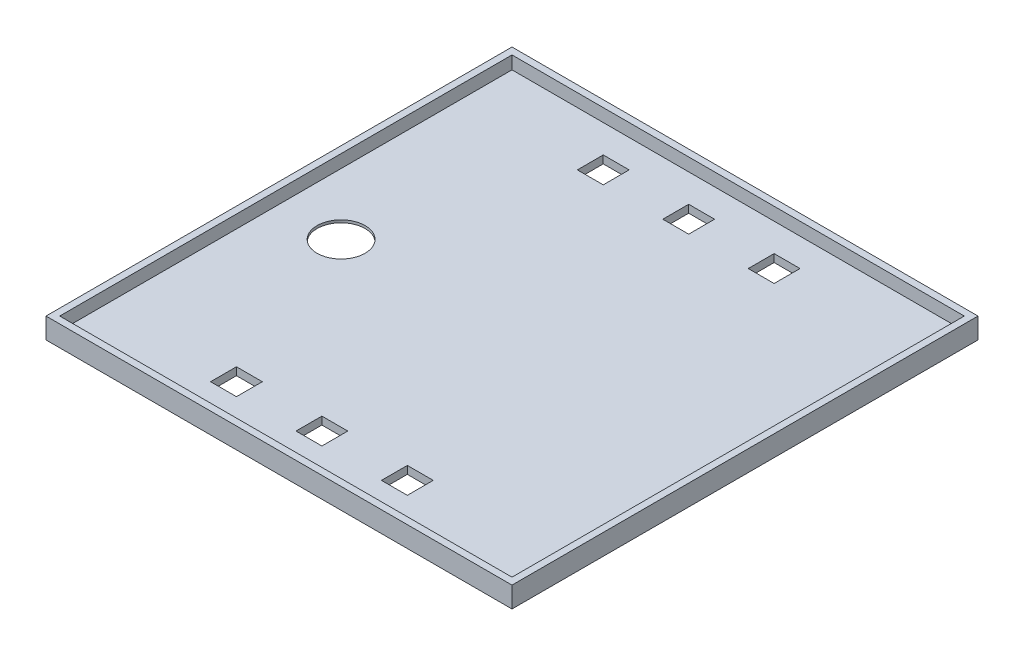
SolidWorks part; units mm, degrees
ref_plane "Front Plane" through (0, 0, 0) normal (0, 0, 1) x (1, 0, 0)
ref_plane "Top Plane" through (0, 0, 0) normal (0, 1, 0) x (1, 0, 0)
ref_plane "Right Plane" through (0, 0, 0) normal (1, 0, 0) x (0, 0, -1)
sketch "Sketch1" plane through (0, 0, 0) normal (0, 1, 0) x (1, 0, 0)
  line L1 (-45, -45) -> (45, -45)
  line L2 (-45, -45) -> (-45, 45)
  line L3 (-45, 45) -> (45, 45)
  line L4 (45, -45) -> (45, 45)
  line L5 (-45, -45) -> (45, 45) construction
  line L6 (-45, 45) -> (45, -45) construction
  point P0 (0, 0)
  dimension "D1" = 90
  dimension "D2" = 90
extrude "Boss-Extrude1" add sketch "Sketch1" along normal blind 4
sketch "Sketch2" plane through (0, 4, 0) normal (0, 1, 0) x (1, 0, 0)
  line L1 (-43.675, -43.675) -> (43.675, -43.675)
  line L2 (-43.675, -43.675) -> (-43.675, 43.675)
  line L3 (-43.675, 43.675) -> (43.675, 43.675)
  line L4 (43.675, -43.675) -> (43.675, 43.675)
  line L5 (-43.675, -43.675) -> (43.675, 43.675) construction
  line L6 (-43.675, 43.675) -> (43.675, -43.675) construction
  point P0 (0, 0)
  dimension "D1" = 87.35
  dimension "D2" = 87.35
extrude "Cut-Extrude2" cut sketch "Sketch2" against normal blind 2.5
sketch "Sketch6" plane through (0, 0, 0) normal (0, -1, 0) x (1, 0, 0)
  line L1 (17.3668, -38.2575) -> (12.3668, -38.2575)
  line L2 (17.3668, -38.2575) -> (17.3668, -33.2575)
  line L3 (17.3668, -33.2575) -> (12.3668, -33.2575)
  line L4 (12.3668, -38.2575) -> (12.3668, -33.2575)
  line L5 (0.8662, -38.2575) -> (-4.1338, -38.2575)
  line L6 (0.8662, -38.2575) -> (0.8662, -33.2575)
  line L7 (0.8662, -33.2575) -> (-4.1338, -33.2575)
  line L8 (-4.1338, -38.2575) -> (-4.1338, -33.2575)
  line L9 (-15.6345, -38.2575) -> (-20.6345, -38.2575)
  line L10 (-15.6345, -38.2575) -> (-15.6345, -33.2575)
  line L11 (-15.6345, -33.2575) -> (-20.6345, -33.2575)
  line L12 (-20.6345, -38.2575) -> (-20.6345, -33.2575)
  line L13 (17.3767, 32.5926) -> (12.3767, 32.5926)
  line L14 (17.3767, 32.5926) -> (17.3767, 37.5926)
  line L15 (17.3767, 37.5926) -> (12.3767, 37.5926)
  line L16 (12.3767, 32.5926) -> (12.3767, 37.5926)
  line L17 (0.876, 32.5926) -> (-4.124, 32.5926)
  line L18 (0.876, 32.5926) -> (0.876, 37.5926)
  line L19 (0.876, 37.5926) -> (-4.124, 37.5926)
  line L20 (-4.124, 32.5926) -> (-4.124, 37.5926)
  line L21 (-15.6246, 32.5926) -> (-20.6246, 32.5926)
  line L22 (-15.6246, 32.5926) -> (-15.6246, 37.5926)
  line L23 (-15.6246, 37.5926) -> (-20.6246, 37.5926)
  line L24 (-20.6246, 32.5926) -> (-20.6246, 37.5926)
  point P36 (0, 0)
  dimension "D1" = 5
  dimension "D2" = 5
  dimension "D3" = 5
extrude "Cut-Extrude5" cut sketch "Sketch6" against normal blind 3
sketch "Sketch7" plane through (0, 0, 0) normal (0, -1, 0) x (1, 0, 0)
  circle A0 centre (-31.8184, 1.19) radius 6.5
  point P3 (0, 0)
extrude "Cut-Extrude6" cut sketch "Sketch7" against normal blind 1
sketch "Sketch8" plane through (0, 1, 0) normal (0, -1, 0) x (1, 0, 0)
  circle A0 centre (-31.8184, 1.19) radius 4.6379
extrude "Cut-Extrude7" cut sketch "Sketch8" against normal blind 2.7
sketch "Sketch9" plane through (0, 0, 0) normal (0, -1, 0) x (1, 0, 0)
  line L0 (-20.6246, 37.5926) -> (-20.6246, 45)
  line L1 (-45, 45) -> (45, 45) construction
  dimension "D1" = 7.4074
sketch "Sketch10" plane through (0, 0, 0) normal (0, -1, 0) x (1, 0, 0)
